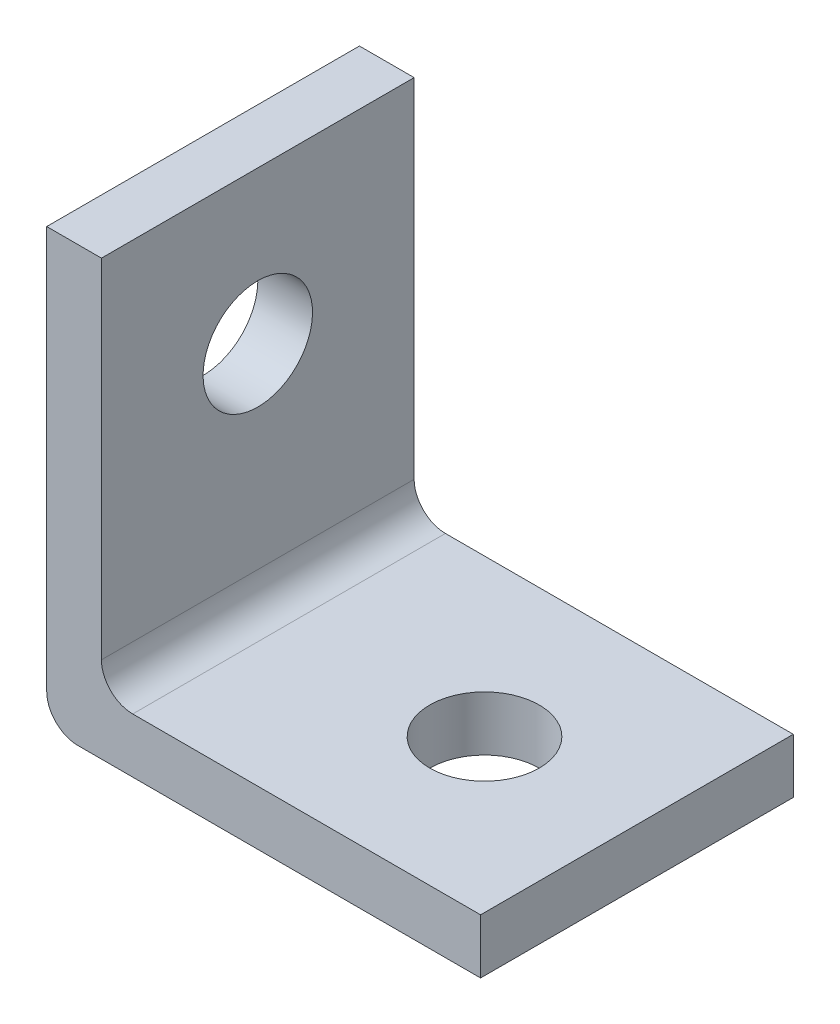
SolidWorks part; units mm, degrees
ref_plane "Front Plane" through (0, 0, 0) normal (0, 0, 1) x (1, 0, 0)
ref_plane "Top Plane" through (0, 0, 0) normal (0, 1, 0) x (1, 0, 0)
ref_plane "Right Plane" through (0, 0, 0) normal (1, 0, 0) x (0, 0, -1)
sketch "Sketch1" plane through (0, 0, 0) normal (0, 0, 1) x (1, 0, 0)
  line L0 (0, 2) -> (0, 50)
  line L1 (0, 50) -> (3.5, 50)
  line L2 (3.5, 50) -> (3.5, 5.5)
  line L3 (5.5, 3.5) -> (50, 3.5)
  line L4 (50, 3.5) -> (50, 0)
  line L5 (50, 0) -> (2, 0)
  arc A0 (3.5, 5.5) -> (5.5, 3.5) centre (5.5, 5.5) ccw
  arc A1 (0, 2) -> (2, 0) centre (2, 2) ccw
  point P12 (0, 0)
  dimension "D3" = 2
  dimension "D1" = 50
  dimension "D2" = 3.5
extrude "Boss-Extrude1" add sketch "Sketch1" along normal blind 20
sketch "Sketch2" plane through (0, 3.5, 0) normal (0, 1, 0) x (1, 0, 0)
  line L1 (50, -20) -> (50, 0) construction
  circle A0 centre (38, -10) radius 3.5
  circle A1 centre (18, -10) radius 3.5
  point P7 (50, -10)
  dimension "D1" = 7
  dimension "D2" = 12
  dimension "D3" = 20
extrude "Cut-Extrude1" cut sketch "Sketch2" against normal through all
sketch "Sketch3" plane through (3.5, 0, 0) normal (1, 0, 0) x (0, 0, -1)
  line L0 (-20, 50) -> (0, 50) construction
  circle A0 centre (-10, 38) radius 3.5
  circle A1 centre (-10, 18) radius 3.5
  point P4 (-10, 50)
  dimension "D1" = 7
  dimension "D2" = 12
  dimension "D3" = 20
extrude "Cut-Extrude2" cut sketch "Sketch3" against normal through all
sketch "Sketch4" plane through (0, 3.5, 0) normal (0, 1, 0) x (1, 0, 0)
  line L0 (50, 0) -> (5.5, 0) construction
  line L1 (27.75, 0) -> (50, 0)
  line L2 (27.75, 0) -> (27.75, -20)
  line L3 (27.75, -20) -> (50, -20)
  line L4 (50, 0) -> (50, -20)
extrude "Cut-Extrude3" cut sketch "Sketch4" against normal through all
sketch "Sketch5" plane through (3.5, 0, 0) normal (1, 0, 0) x (0, 0, -1)
  line L0 (0, 5.5) -> (0, 50) construction
  line L1 (-20, 50) -> (0, 50)
  line L2 (-20, 50) -> (-20, 27.75)
  line L3 (-20, 27.75) -> (0, 27.75)
  line L4 (0, 50) -> (0, 27.75)
extrude "Cut-Extrude4" cut sketch "Sketch5" against normal through all
